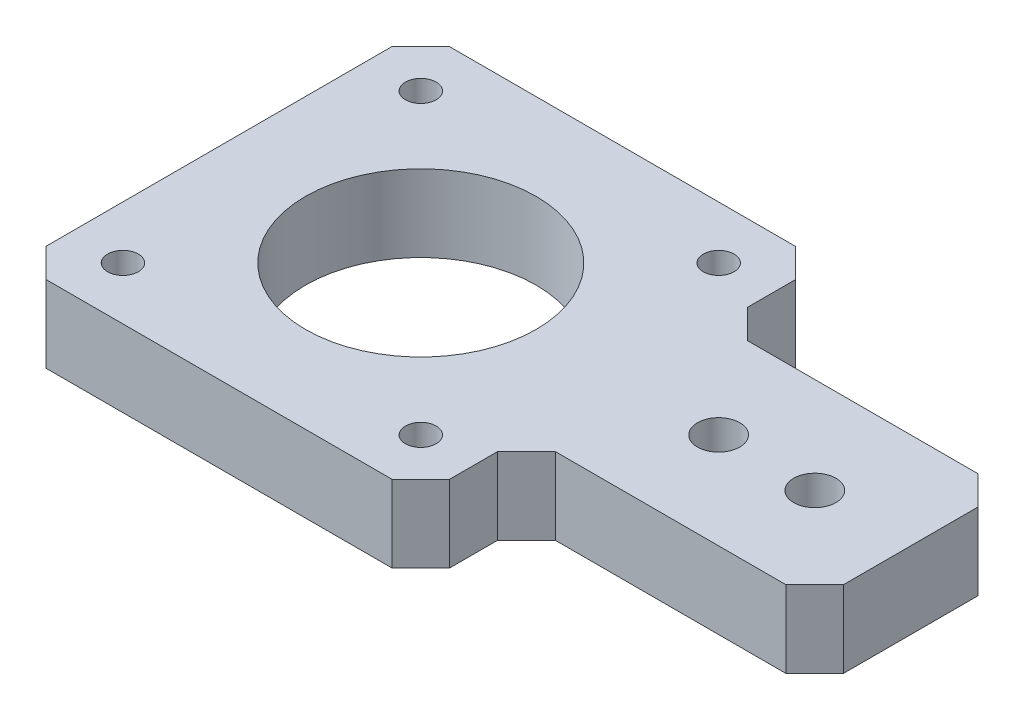
SolidWorks part; units mm, degrees
ref_plane "Alzado" through (0, 0, 0) normal (0, 0, 1) x (1, 0, 0)
ref_plane "Planta" through (0, 0, 0) normal (0, 1, 0) x (1, 0, 0)
ref_plane "Vista lateral" through (0, 0, 0) normal (1, 0, 0) x (0, 0, -1)
sketch "Croquis1" plane through (0, 0, 0) normal (0, 1, 0) x (1, 0, 0)
  line L1 (18, -21) -> (20.9981, -18.0019)
  line L2 (20.9981, -18.0019) -> (20.9981, -13.0019)
  line L3 (20.9981, -13.0019) -> (23.9963, -10.0037)
  line L5 (47.9963, -10.0037) -> (50.9944, -7.0056)
  line L6 (50.9944, -7.0056) -> (50.9944, 6.9944)
  line L7 (50.9944, 6.9944) -> (47.9963, 9.9925)
  line L8 (47.9963, 9.9925) -> (23.9963, 9.9925)
  line L9 (23.9963, 9.9925) -> (20.9981, 12.9907)
  line L10 (20.9981, 12.9907) -> (20.9981, 17.9907)
  line L11 (20.9981, 17.9907) -> (18, 20.9888)
  line L12 (18, 20.9888) -> (-18, 20.9888)
  line L13 (-18, 20.9888) -> (-21.0019, 17.9944)
  line L14 (-21.0019, 17.9944) -> (-21.0019, -18.0056)
  line L15 (-21.0019, -18.0056) -> (-18, -21)
  line L16 (-18, -21) -> (18, -21)
  line L17 (23.9963, -10.0037) -> (47.9963, -10.0037)
  line L18 (0, -21) -> (0, 0) construction
  line L19 (0, 0) -> (30.9981, -0.0037) construction
  line L20 (-15.5, 15.5) -> (15.5, 15.5) construction
  line L21 (-15.5, 15.5) -> (-15.5, -15.5) construction
  line L22 (-15.5, -15.5) -> (15.5, -15.5) construction
  line L23 (15.5, 15.5) -> (15.5, -15.5) construction
  line L24 (30.9981, -0.0037) -> (41.0081, -0.0037) construction
  line L25 (0, 0) -> (0, 15.5) construction
  line L26 (30.9981, -0.0037) -> (30.9981, 9.9925) construction
  line L27 (0, 15.5) -> (0, 20.9888) construction
  circle A0 centre (0, 0) radius 12
  circle A1 centre (-15.5, -15.5) radius 1.6
  circle A2 centre (-15.5, 15.5) radius 1.6
  circle A3 centre (15.5, 15.5) radius 1.6
  circle A4 centre (15.5, -15.5) radius 1.6
  circle A5 centre (30.9981, -0.0037) radius 2.2
  circle A6 centre (41.0081, -0.0037) radius 2.2
  point P31 (0, 0)
  point P34 (0, 0)
  dimension "D1" = 3.0019
  dimension "D3" = 135
  dimension "D4" = 5
  dimension "D5" = 2.9981
  dimension "D6" = 2.9981
  dimension "D17" = 24
  dimension "D20" = 3.2
  dimension "D21" = 3.2
  dimension "D22" = 3.2
  dimension "D23" = 3.2
  dimension "D26" = 4.4
  dimension "D27" = 4.4
  dimension "D2" = 36
  dimension "D7" = 24
  dimension "D8" = 2.9981
  dimension "D9" = 14
  dimension "D10" = 2.9981
  dimension "D11" = 24
  dimension "D12" = 2.9981
  dimension "D13" = 5
  dimension "D14" = 2.9981
  dimension "D15" = 36
  dimension "D16" = 36
  dimension "D18" = 21
  dimension "D19" = 31
  dimension "D24" = 30.9981
  dimension "D25" = 10.01
  dimension "D28" = 15.5
  dimension "D29" = 9.9963
  dimension "D30" = 5.4888
  dimension "D31" = 135.071
  dimension "D32" = 134.929
  dimension "D33" = 135
extrude "Saliente-Extruir1" add sketch "Croquis1" along normal blind 8
